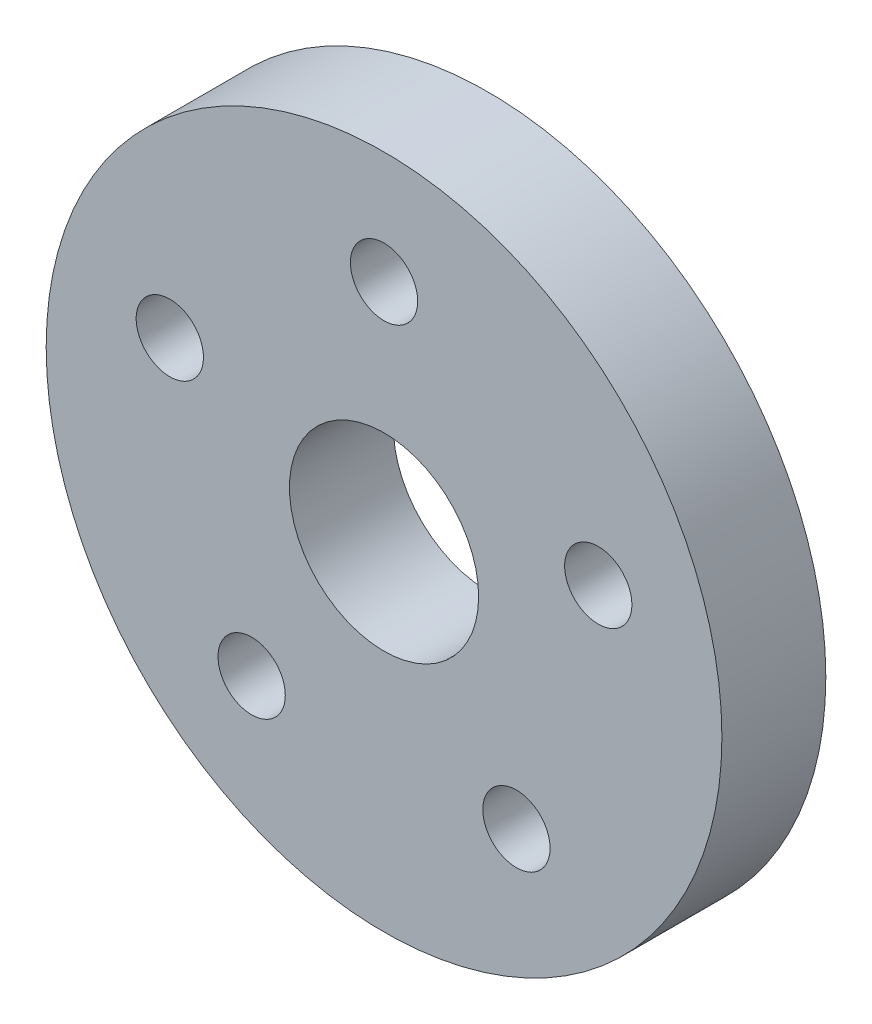
SolidWorks part; units mm, degrees
ref_plane "Front Plane" through (0, 0, 0) normal (0, 0, 1) x (1, 0, 0)
ref_plane "Top Plane" through (0, 0, 0) normal (0, 1, 0) x (1, 0, 0)
ref_plane "Right Plane" through (0, 0, 0) normal (1, 0, 0) x (0, 0, -1)
sketch "Sketch1" plane through (0, 0, 0) normal (0, 0, 1) x (1, 0, 0)
  circle A0 centre (0, 0) radius 14.2875
  circle A1 centre (0, 0) radius 4
  circle A2 centre (0, 9.525) radius 1.4224
  circle A3 centre (9.0588, 2.9434) radius 1.4224
  circle A4 centre (5.5987, -7.7059) radius 1.4224
  circle A5 centre (-5.5987, -7.7059) radius 1.4224
  circle A6 centre (-9.0588, 2.9434) radius 1.4224
  point P17 (0, 0)
  dimension "D1" = 28.575
  dimension "D2" = 8
  dimension "D3" = 2.8448
  dimension "D4" = 9.525
  dimension "D5" = 5
extrude "Boss-Extrude1" add sketch "Sketch1" along normal blind 4.3942
